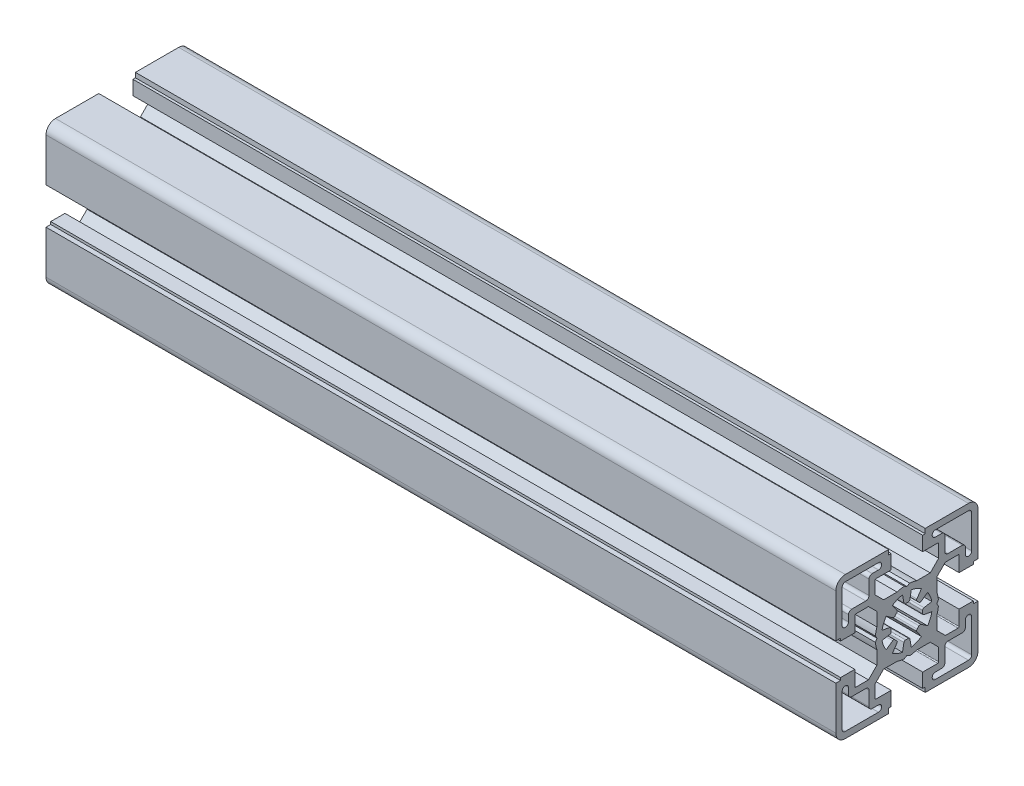
SolidWorks part; units mm, degrees
ref_plane "Спереди" through (0, 0, 0) normal (0, 0, 1) x (1, 0, 0)
ref_plane "Сверху" through (0, 0, 0) normal (0, 1, 0) x (1, 0, 0)
ref_plane "Справа" through (0, 0, 0) normal (1, 0, 0) x (0, 0, -1)
sketch "Эскиз2" plane through (0, 0, 0) normal (1, 0, 0) x (0, 0, -1)
  line L0 (-0.9511, 5.394) -> (-1.3892, 7.8785)
  line L1 (-3.1416, 4.4867) -> (-4.5886, 6.5532)
  line L2 (-4.4867, 3.1416) -> (-6.5532, 4.5886)
  line L3 (7.8785, -1.3892) -> (5.394, -0.9511)
  line L4 (-5.394, 0.9511) -> (-7.8785, 1.3892)
  line L5 (16.5, 5) -> (21, 5)
  line L6 (-21, 5) -> (-16.5, 5)
  line L7 (21, 5.8) -> (22.5, 5.8)
  line L8 (-22.5, 5.8) -> (-21, 5.8)
  line L9 (3.1225, 9.5) -> (7.3787, 9.5)
  line L10 (-7.3787, 9.5) -> (-3.1225, 9.5)
  line L11 (12.1713, 10.05) -> (16.2, 10.05)
  line L12 (-16.2, 10.05) -> (-12.1713, 10.05)
  line L13 (-17.5, 12) -> (-13, 12)
  line L14 (5, 16.5) -> (9.75, 16.5)
  line L15 (-9.75, 16.5) -> (-5, 16.5)
  line L16 (-19.5, 20.5) -> (-9, 20.5)
  line L17 (5, 21) -> (5.8, 21)
  line L18 (-5.8, 21) -> (-5, 21)
  line L19 (5.8, 22.5) -> (19.5, 22.5)
  line L20 (-19.5, 22.5) -> (-5.8, 22.5)
  line L21 (-7.8785, -1.3892) -> (-5.394, -0.9511)
  line L22 (5.394, 0.9511) -> (7.8785, 1.3892)
  line L23 (4.4867, 3.1416) -> (6.5532, 4.5886)
  line L24 (3.1416, 4.4867) -> (4.5886, 6.5532)
  line L25 (0.9511, 5.394) -> (1.3892, 7.8785)
  line L26 (-22.5, 5.8) -> (-22.5, 19.5)
  line L27 (-21, 5) -> (-21, 5.8)
  line L28 (-20.5, 9) -> (-20.5, 19.5)
  line L29 (-16.5, 5) -> (-16.5, 9.75)
  line L30 (-12, 13) -> (-12, 17.5)
  line L31 (-5.8, 21) -> (-5.8, 22.5)
  line L32 (-5, 16.5) -> (-5, 21)
  line L33 (5, 16.5) -> (5, 21)
  line L34 (5.8, 21) -> (5.8, 22.5)
  line L35 (9.5, 3.1225) -> (9.5, 7.3787)
  line L36 (10.05, 12.1713) -> (10.05, 16.2)
  line L37 (16.5, 5) -> (16.5, 9.75)
  line L38 (21, 5) -> (21, 5.8)
  line L39 (22.5, 5.8) -> (22.5, 19.5)
  line L40 (1.3892, -7.8785) -> (0.9511, -5.394)
  line L41 (4.5886, -6.5532) -> (3.1416, -4.4867)
  line L42 (6.5532, -4.5886) -> (4.4867, -3.1416)
  line L43 (-7.3787, -9.5) -> (-3.1225, -9.5)
  line L44 (3.1225, -9.5) -> (7.3787, -9.5)
  line L45 (-6.5532, -4.5886) -> (-4.4867, -3.1416)
  line L46 (-4.5886, -6.5532) -> (-3.1416, -4.4867)
  line L47 (-1.3892, -7.8785) -> (-0.9511, -5.394)
  line L48 (-9.5, -7.3787) -> (-9.5, -3.1225)
  line L49 (9.5, -7.3787) -> (9.5, -3.1225)
  line L50 (-22.5, -5.8) -> (-21, -5.8)
  line L51 (-21, -5) -> (-16.5, -5)
  line L52 (-21, -5.8) -> (-21, -5)
  line L53 (-16.5, -9.75) -> (-16.5, -5)
  line L54 (-22.5, -19.5) -> (-22.5, -5.8)
  line L55 (21, -5.8) -> (22.5, -5.8)
  line L56 (16.5, -5) -> (21, -5)
  line L57 (21, -5.8) -> (21, -5)
  line L58 (16.5, -9.75) -> (16.5, -5)
  line L59 (12.1713, -10.05) -> (16.2, -10.05)
  line L60 (22.5, -19.5) -> (22.5, -5.8)
  line L61 (-16.2, -10.05) -> (-12.1713, -10.05)
  line L62 (5, -16.5) -> (9.75, -16.5)
  line L63 (-9.75, -16.5) -> (-5, -16.5)
  line L64 (5, -21) -> (5.8, -21)
  line L65 (-5.8, -21) -> (-5, -21)
  line L66 (5.8, -22.5) -> (19.5, -22.5)
  line L67 (-19.5, -22.5) -> (-5.8, -22.5)
  line L68 (-10.05, -12.1713) -> (-10.05, -16.2)
  line L69 (-5.8, -21) -> (-5.8, -22.5)
  line L70 (-5, -16.5) -> (-5, -21)
  line L71 (5, -16.5) -> (5, -21)
  line L72 (5.8, -21) -> (5.8, -22.5)
  line L73 (10.05, -12.1713) -> (10.05, -16.2)
  line L74 (-9.5, 3.1225) -> (-9.5, 7.3787)
  line L75 (-9.5, 7.3787) -> (-12.1713, 10.05)
  line L76 (7.3787, 9.5) -> (10.05, 12.1713)
  line L77 (9.5, 7.3787) -> (12.1713, 10.05)
  line L78 (9.5, -7.3787) -> (12.1713, -10.05)
  line L79 (7.3787, -9.5) -> (10.05, -12.1713)
  line L80 (-7.3787, -9.5) -> (-10.05, -12.1713)
  line L81 (-12.1713, -10.05) -> (-9.5, -7.3787)
  line L82 (-10.05, 12.1713) -> (-10.05, 16.2)
  line L83 (-10.05, 12.1713) -> (-7.3787, 9.5)
  line L84 (-9.4624, 0) -> (-9.9624, 0.866)
  line L85 (-9.4624, 0) -> (-9.9624, -0.866)
  line L86 (0, -9.4624) -> (-0.866, -9.9624)
  line L87 (0, -9.4624) -> (0.866, -9.9624)
  line L88 (0, 9.4624) -> (0.866, 9.9624)
  line L89 (0, 9.4624) -> (-0.866, 9.9624)
  line L90 (9.4624, 0) -> (9.9624, -0.866)
  line L91 (9.4624, 0) -> (9.9624, 0.866)
  line L92 (-11, 18.5) -> (-9, 18.5)
  line L93 (-18.5, 11) -> (-18.5, 9)
  line L94 (17.5, 12) -> (13, 12)
  line L95 (12, 13) -> (12, 17.5)
  line L96 (19.5, 20.5) -> (9, 20.5)
  line L97 (11, 18.5) -> (9, 18.5)
  line L98 (20.5, 9) -> (20.5, 19.5)
  line L99 (18.5, 11) -> (18.5, 9)
  line L100 (-17.5, -12) -> (-13, -12)
  line L101 (-12, -13) -> (-12, -17.5)
  line L102 (-19.5, -20.5) -> (-9, -20.5)
  line L103 (-11, -18.5) -> (-9, -18.5)
  line L104 (-20.5, -9) -> (-20.5, -19.5)
  line L105 (-18.5, -11) -> (-18.5, -9)
  line L106 (19.5, -20.5) -> (9, -20.5)
  line L107 (11, -18.5) -> (9, -18.5)
  line L108 (17.5, -12) -> (13, -12)
  line L109 (12, -13) -> (12, -17.5)
  line L110 (20.5, -9) -> (20.5, -19.5)
  line L111 (18.5, -11) -> (18.5, -9)
  arc A0 (-19.5, 20.5) -> (-20.5, 19.5) centre (-19.5, 19.5) ccw
  arc A1 (-19.5, 22.5) -> (-22.5, 19.5) centre (-19.5, 19.5) ccw
  arc A2 (-13, 12) -> (-12, 13) centre (-13, 13) ccw
  arc A3 (-3.2283, 3.8181) -> (-3.8181, 3.2283) centre (0, 0) ccw
  arc A4 (3.8181, 3.2283) -> (3.2283, 3.8181) centre (0, 0) ccw
  arc A5 (-4.9826, 0.417) -> (-4.9826, -0.417) centre (0, 0) ccw
  arc A6 (0.417, 4.9826) -> (-0.417, 4.9826) centre (0, 0) ccw
  arc A7 (4.9826, -0.417) -> (4.9826, 0.417) centre (0, 0) ccw
  arc A8 (-6.5532, 4.5886) -> (-7.8785, 1.3892) centre (0, 0) ccw
  arc A9 (-1.3892, 7.8785) -> (-4.5886, 6.5532) centre (0, 0) ccw
  arc A10 (4.5886, 6.5532) -> (1.3892, 7.8785) centre (0, 0) ccw
  arc A11 (7.8785, 1.3892) -> (6.5532, 4.5886) centre (0, 0) ccw
  arc A12 (22.5, 19.5) -> (19.5, 22.5) centre (19.5, 19.5) ccw
  arc A13 (3.2283, -3.8181) -> (3.8181, -3.2283) centre (0, 0) ccw
  arc A14 (-3.8181, -3.2283) -> (-3.2283, -3.8181) centre (0, 0) ccw
  arc A15 (-0.417, -4.9826) -> (0.417, -4.9826) centre (0, 0) ccw
  arc A16 (6.5532, -4.5886) -> (7.8785, -1.3892) centre (0, 0) ccw
  arc A17 (1.3892, -7.8785) -> (4.5886, -6.5532) centre (0, 0) ccw
  arc A18 (-4.5886, -6.5532) -> (-1.3892, -7.8785) centre (0, 0) ccw
  arc A19 (-7.8785, -1.3892) -> (-6.5532, -4.5886) centre (0, 0) ccw
  arc A20 (-22.5, -19.5) -> (-19.5, -22.5) centre (-19.5, -19.5) ccw
  arc A21 (19.5, -22.5) -> (22.5, -19.5) centre (19.5, -19.5) ccw
  arc A22 (-4.4867, 3.1416) -> (-3.8181, 3.2283) centre (-4.1999, 3.5512) ccw
  arc A23 (-3.2283, 3.8181) -> (-3.1416, 4.4867) centre (-3.5512, 4.1999) ccw
  arc A24 (-0.9511, 5.394) -> (-0.417, 4.9826) centre (-0.4587, 5.4808) ccw
  arc A25 (0.417, 4.9826) -> (0.9511, 5.394) centre (0.4587, 5.4808) ccw
  arc A26 (3.1416, 4.4867) -> (3.2283, 3.8181) centre (3.5512, 4.1999) ccw
  arc A27 (3.8181, 3.2283) -> (4.4867, 3.1416) centre (4.1999, 3.5512) ccw
  arc A28 (5.394, 0.9511) -> (4.9826, 0.417) centre (5.4808, 0.4587) ccw
  arc A29 (4.9826, -0.417) -> (5.394, -0.9511) centre (5.4808, -0.4587) ccw
  arc A30 (4.4867, -3.1416) -> (3.8181, -3.2283) centre (4.1999, -3.5512) ccw
  arc A31 (3.2283, -3.8181) -> (3.1416, -4.4867) centre (3.5512, -4.1999) ccw
  arc A32 (0.9511, -5.394) -> (0.417, -4.9826) centre (0.4587, -5.4808) ccw
  arc A33 (-0.417, -4.9826) -> (-0.9511, -5.394) centre (-0.4587, -5.4808) ccw
  arc A34 (-3.1416, -4.4867) -> (-3.2283, -3.8181) centre (-3.5512, -4.1999) ccw
  arc A35 (-3.8181, -3.2283) -> (-4.4867, -3.1416) centre (-4.1999, -3.5512) ccw
  arc A36 (-5.394, -0.9511) -> (-4.9826, -0.417) centre (-5.4808, -0.4587) ccw
  arc A37 (-4.9826, 0.417) -> (-5.394, 0.9511) centre (-5.4808, 0.4587) ccw
  arc A38 (-16.5, -9.75) -> (-16.2, -10.05) centre (-16.2, -9.75) ccw
  arc A39 (-10.05, -16.2) -> (-9.75, -16.5) centre (-9.75, -16.2) ccw
  arc A40 (9.75, -16.5) -> (10.05, -16.2) centre (9.75, -16.2) ccw
  arc A41 (16.2, -10.05) -> (16.5, -9.75) centre (16.2, -9.75) ccw
  arc A42 (16.5, 9.75) -> (16.2, 10.05) centre (16.2, 9.75) ccw
  arc A43 (10.05, 16.2) -> (9.75, 16.5) centre (9.75, 16.2) ccw
  arc A44 (-9.75, 16.5) -> (-10.05, 16.2) centre (-9.75, 16.2) ccw
  arc A45 (-16.2, 10.05) -> (-16.5, 9.75) centre (-16.2, 9.75) ccw
  arc A46 (-9.9624, -0.866) -> (-9.5, -3.1225) centre (0, 0) ccw
  arc A47 (-9.5, 3.1225) -> (-9.9624, 0.866) centre (0, 0) ccw
  arc A48 (-3.1225, -9.5) -> (-0.866, -9.9624) centre (0, 0) ccw
  arc A49 (3.1225, 9.5) -> (0.866, 9.9624) centre (0, 0) ccw
  arc A50 (9.5, -3.1225) -> (9.9624, -0.866) centre (0, 0) ccw
  arc A51 (-0.866, 9.9624) -> (-3.1225, 9.5) centre (0, 0) ccw
  arc A52 (9.9624, 0.866) -> (9.5, 3.1225) centre (0, 0) ccw
  arc A53 (0.866, -9.9624) -> (3.1225, -9.5) centre (0, 0) ccw
  arc A54 (-11, 18.5) -> (-12, 17.5) centre (-11, 17.5) ccw
  arc A55 (-9, 18.5) -> (-9, 20.5) centre (-9, 19.5) ccw
  arc A56 (-17.5, 12) -> (-18.5, 11) centre (-17.5, 11) ccw
  arc A57 (-20.5, 9) -> (-18.5, 9) centre (-19.5, 9) ccw
  arc A58 (20.5, 19.5) -> (19.5, 20.5) centre (19.5, 19.5) ccw
  arc A59 (12, 13) -> (13, 12) centre (13, 13) ccw
  arc A60 (12, 17.5) -> (11, 18.5) centre (11, 17.5) ccw
  arc A61 (18.5, 11) -> (17.5, 12) centre (17.5, 11) ccw
  arc A62 (9, 20.5) -> (9, 18.5) centre (9, 19.5) ccw
  arc A63 (18.5, 9) -> (20.5, 9) centre (19.5, 9) ccw
  arc A64 (-20.5, -19.5) -> (-19.5, -20.5) centre (-19.5, -19.5) ccw
  arc A65 (-12, -13) -> (-13, -12) centre (-13, -13) ccw
  arc A66 (-12, -17.5) -> (-11, -18.5) centre (-11, -17.5) ccw
  arc A67 (-18.5, -11) -> (-17.5, -12) centre (-17.5, -11) ccw
  arc A68 (-9, -20.5) -> (-9, -18.5) centre (-9, -19.5) ccw
  arc A69 (-18.5, -9) -> (-20.5, -9) centre (-19.5, -9) ccw
  arc A70 (19.5, -20.5) -> (20.5, -19.5) centre (19.5, -19.5) ccw
  arc A71 (11, -18.5) -> (12, -17.5) centre (11, -17.5) ccw
  arc A72 (9, -18.5) -> (9, -20.5) centre (9, -19.5) ccw
  arc A73 (13, -12) -> (12, -13) centre (13, -13) ccw
  arc A74 (17.5, -12) -> (18.5, -11) centre (17.5, -11) ccw
  arc A75 (20.5, -9) -> (18.5, -9) centre (19.5, -9) ccw
extrude "Бобышка-Вытянуть1" add sketch "Эскиз2" along normal blind 250 contours L75 L12 A45 L29 L6 L27 L8 L26 A1 L20 L31 L18 L32 L15 A44 L82 L83 L10 A51 L89 L88 A49 L9 L76 L36 A43 L14 L33 L17 L34 L19 A12 L39 L7 L38 L5 L37 A42 L11 L77 L35 A52 L91 L90 A50 L49 L78 L59 A41 L58 L56 L57 L55 L60 A21 L66 L72 L64 L71 L62 A40 L73 L79 L44 A53 L87 L86 A48 L43 L80 L68 A39 L63 L70 L65 L69 L67 A20 L54 L50 L52 L51 L53 A38 L61 L81 L48 A46 L85 L84 A47 L74
sketch "Эскиз3" plane through (0, 0, 0) normal (-1, 0, 0) x (0, 0, 1)
  line L0 (-0.9511, 5.394) -> (-1.3892, 7.8785)
  line L1 (-3.1416, 4.4867) -> (-4.5886, 6.5532)
  line L2 (-4.4867, 3.1416) -> (-6.5532, 4.5886)
  line L3 (7.8785, -1.3892) -> (5.394, -0.9511)
  line L4 (-5.394, 0.9511) -> (-7.8785, 1.3892)
  line L13 (-17.5, 12) -> (-13, 12)
  line L16 (-19.5, 20.5) -> (-9, 20.5)
  line L21 (-7.8785, -1.3892) -> (-5.394, -0.9511)
  line L22 (5.394, 0.9511) -> (7.8785, 1.3892)
  line L23 (4.4867, 3.1416) -> (6.5532, 4.5886)
  line L24 (3.1416, 4.4867) -> (4.5886, 6.5532)
  line L25 (0.9511, 5.394) -> (1.3892, 7.8785)
  line L28 (-20.5, 9) -> (-20.5, 19.5)
  line L30 (-12, 13) -> (-12, 17.5)
  line L40 (1.3892, -7.8785) -> (0.9511, -5.394)
  line L41 (4.5886, -6.5532) -> (3.1416, -4.4867)
  line L42 (6.5532, -4.5886) -> (4.4867, -3.1416)
  line L45 (-6.5532, -4.5886) -> (-4.4867, -3.1416)
  line L46 (-4.5886, -6.5532) -> (-3.1416, -4.4867)
  line L47 (-1.3892, -7.8785) -> (-0.9511, -5.394)
  line L92 (-11, 18.5) -> (-9, 18.5)
  line L93 (-18.5, 11) -> (-18.5, 9)
  line L94 (17.5, 12) -> (13, 12)
  line L95 (12, 13) -> (12, 17.5)
  line L96 (19.5, 20.5) -> (9, 20.5)
  line L97 (11, 18.5) -> (9, 18.5)
  line L98 (20.5, 9) -> (20.5, 19.5)
  line L99 (18.5, 11) -> (18.5, 9)
  line L100 (-17.5, -12) -> (-13, -12)
  line L101 (-12, -13) -> (-12, -17.5)
  line L102 (-19.5, -20.5) -> (-9, -20.5)
  line L103 (-11, -18.5) -> (-9, -18.5)
  line L104 (-20.5, -9) -> (-20.5, -19.5)
  line L105 (-18.5, -11) -> (-18.5, -9)
  line L106 (19.5, -20.5) -> (9, -20.5)
  line L107 (11, -18.5) -> (9, -18.5)
  line L108 (17.5, -12) -> (13, -12)
  line L109 (12, -13) -> (12, -17.5)
  line L110 (20.5, -9) -> (20.5, -19.5)
  line L111 (18.5, -11) -> (18.5, -9)
  arc A0 (-19.5, 20.5) -> (-20.5, 19.5) centre (-19.5, 19.5) ccw
  arc A2 (-13, 12) -> (-12, 13) centre (-13, 13) ccw
  arc A3 (-3.2283, 3.8181) -> (-3.8181, 3.2283) centre (0, 0) ccw
  arc A4 (3.8181, 3.2283) -> (3.2283, 3.8181) centre (0, 0) ccw
  arc A5 (-4.9826, 0.417) -> (-4.9826, -0.417) centre (0, 0) ccw
  arc A6 (0.417, 4.9826) -> (-0.417, 4.9826) centre (0, 0) ccw
  arc A7 (4.9826, -0.417) -> (4.9826, 0.417) centre (0, 0) ccw
  arc A8 (-6.5532, 4.5886) -> (-7.8785, 1.3892) centre (0, 0) ccw
  arc A9 (-1.3892, 7.8785) -> (-4.5886, 6.5532) centre (0, 0) ccw
  arc A10 (4.5886, 6.5532) -> (1.3892, 7.8785) centre (0, 0) ccw
  arc A11 (7.8785, 1.3892) -> (6.5532, 4.5886) centre (0, 0) ccw
  arc A13 (3.2283, -3.8181) -> (3.8181, -3.2283) centre (0, 0) ccw
  arc A14 (-3.8181, -3.2283) -> (-3.2283, -3.8181) centre (0, 0) ccw
  arc A15 (-0.417, -4.9826) -> (0.417, -4.9826) centre (0, 0) ccw
  arc A16 (6.5532, -4.5886) -> (7.8785, -1.3892) centre (0, 0) ccw
  arc A17 (1.3892, -7.8785) -> (4.5886, -6.5532) centre (0, 0) ccw
  arc A18 (-4.5886, -6.5532) -> (-1.3892, -7.8785) centre (0, 0) ccw
  arc A19 (-7.8785, -1.3892) -> (-6.5532, -4.5886) centre (0, 0) ccw
  arc A22 (-4.4867, 3.1416) -> (-3.8181, 3.2283) centre (-4.1999, 3.5512) ccw
  arc A23 (-3.2283, 3.8181) -> (-3.1416, 4.4867) centre (-3.5512, 4.1999) ccw
  arc A24 (-0.9511, 5.394) -> (-0.417, 4.9826) centre (-0.4587, 5.4808) ccw
  arc A25 (0.417, 4.9826) -> (0.9511, 5.394) centre (0.4587, 5.4808) ccw
  arc A26 (3.1416, 4.4867) -> (3.2283, 3.8181) centre (3.5512, 4.1999) ccw
  arc A27 (3.8181, 3.2283) -> (4.4867, 3.1416) centre (4.1999, 3.5512) ccw
  arc A28 (5.394, 0.9511) -> (4.9826, 0.417) centre (5.4808, 0.4587) ccw
  arc A29 (4.9826, -0.417) -> (5.394, -0.9511) centre (5.4808, -0.4587) ccw
  arc A30 (4.4867, -3.1416) -> (3.8181, -3.2283) centre (4.1999, -3.5512) ccw
  arc A31 (3.2283, -3.8181) -> (3.1416, -4.4867) centre (3.5512, -4.1999) ccw
  arc A32 (0.9511, -5.394) -> (0.417, -4.9826) centre (0.4587, -5.4808) ccw
  arc A33 (-0.417, -4.9826) -> (-0.9511, -5.394) centre (-0.4587, -5.4808) ccw
  arc A34 (-3.1416, -4.4867) -> (-3.2283, -3.8181) centre (-3.5512, -4.1999) ccw
  arc A35 (-3.8181, -3.2283) -> (-4.4867, -3.1416) centre (-4.1999, -3.5512) ccw
  arc A36 (-5.394, -0.9511) -> (-4.9826, -0.417) centre (-5.4808, -0.4587) ccw
  arc A37 (-4.9826, 0.417) -> (-5.394, 0.9511) centre (-5.4808, 0.4587) ccw
  arc A54 (-11, 18.5) -> (-12, 17.5) centre (-11, 17.5) ccw
  arc A55 (-9, 18.5) -> (-9, 20.5) centre (-9, 19.5) ccw
  arc A56 (-17.5, 12) -> (-18.5, 11) centre (-17.5, 11) ccw
  arc A57 (-20.5, 9) -> (-18.5, 9) centre (-19.5, 9) ccw
  arc A58 (20.5, 19.5) -> (19.5, 20.5) centre (19.5, 19.5) ccw
  arc A59 (12, 13) -> (13, 12) centre (13, 13) ccw
  arc A60 (12, 17.5) -> (11, 18.5) centre (11, 17.5) ccw
  arc A61 (18.5, 11) -> (17.5, 12) centre (17.5, 11) ccw
  arc A62 (9, 20.5) -> (9, 18.5) centre (9, 19.5) ccw
  arc A63 (18.5, 9) -> (20.5, 9) centre (19.5, 9) ccw
  arc A64 (-20.5, -19.5) -> (-19.5, -20.5) centre (-19.5, -19.5) ccw
  arc A65 (-12, -13) -> (-13, -12) centre (-13, -13) ccw
  arc A66 (-12, -17.5) -> (-11, -18.5) centre (-11, -17.5) ccw
  arc A67 (-18.5, -11) -> (-17.5, -12) centre (-17.5, -11) ccw
  arc A68 (-9, -20.5) -> (-9, -18.5) centre (-9, -19.5) ccw
  arc A69 (-18.5, -9) -> (-20.5, -9) centre (-19.5, -9) ccw
  arc A70 (19.5, -20.5) -> (20.5, -19.5) centre (19.5, -19.5) ccw
  arc A71 (11, -18.5) -> (12, -17.5) centre (11, -17.5) ccw
  arc A72 (9, -18.5) -> (9, -20.5) centre (9, -19.5) ccw
  arc A73 (13, -12) -> (12, -13) centre (13, -13) ccw
  arc A74 (17.5, -12) -> (18.5, -11) centre (17.5, -11) ccw
  arc A75 (20.5, -9) -> (18.5, -9) centre (19.5, -9) ccw
extrude "Вырез-Вытянуть1" cut sketch "Эскиз3" against normal through all
